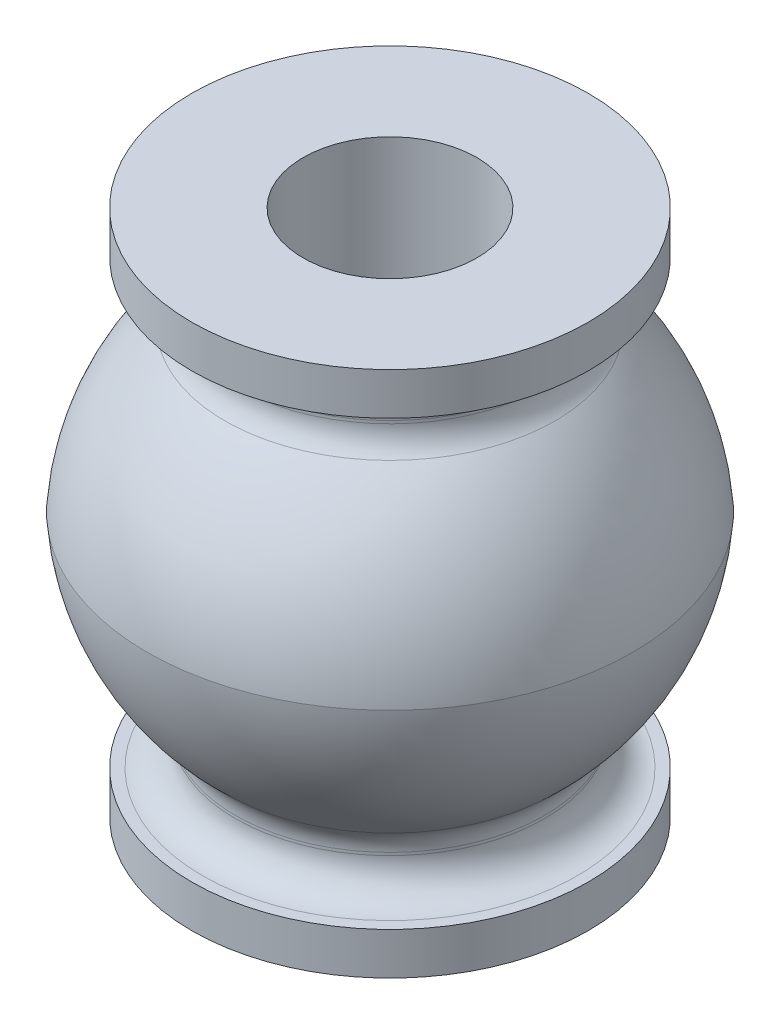
SolidWorks part; units mm, degrees
material "Rubber"
ref_plane "Front" through (0, 0, 0) normal (0, 0, 1) x (1, 0, 0)
ref_plane "Top" through (0, 0, 0) normal (0, 1, 0) x (1, 0, 0)
ref_plane "Right" through (0, 0, 0) normal (1, 0, 0) x (0, 0, -1)
sketch "Sketch2" plane through (0, 0, 0) normal (0, 0, 1) x (1, 0, 0)
  line L0 (0, -8) -> (0, 8) construction
  line L1 (0, 8) -> (2.64, 8) construction
  line L2 (2.64, 8) -> (6.02, 8)
  line L3 (6.02, 8) -> (6.02, 6.72)
  line L4 (6.02, 6.72) -> (4.69, 6.72)
  line L5 (4.69, 6.72) -> (4.69, 5.18)
  line L6 (0, 0) -> (7.375, 0) construction
  line L7 (2.64, 8) -> (2.64, 4.0052)
  line L8 (3.7256, 4.0052) -> (2.64, 4.0052)
  line L9 (0, -8) -> (2.64, -8) construction
  line L10 (3.7256, -4.0052) -> (2.64, -4.0052)
  line L11 (2.64, -8) -> (2.64, -4.0052)
  line L12 (4.69, -6.72) -> (4.69, -5.18)
  line L13 (6.02, -6.72) -> (4.69, -6.72)
  line L14 (6.02, -8) -> (6.02, -6.72)
  line L15 (2.64, -8) -> (6.02, -8)
  arc A0 (4.69, 5.18) -> (7.375, 0) centre (-0.0053, -0.5396) cw
  arc A1 (3.7256, 4.0052) -> (5.8499, 0) centre (-0.0053, -0.5396) cw
  arc A2 (3.7256, 4.0052) -> (5.859, -0.1108) centre (-0.0053, -0.5396) cw construction
  arc A3 (3.7256, -4.0052) -> (5.8499, 0) centre (-0.0053, 0.5396) ccw
  arc A4 (4.69, -5.18) -> (7.375, 0) centre (-0.0053, 0.5396) ccw
  dimension "D7" = 7.4
  dimension "D1" = 6.02
  dimension "D2" = 8
  dimension "D3" = 2.64
  dimension "D4" = 9.38
  dimension "D5" = 1.28
  dimension "D6" = 7.375
  dimension "D8" = 1.54
  dimension "D9" = 1.52
revolve "Revolve1" add sketch "Sketch2" angle 360 about L0
fillet "Fillet1" radius 1 4 edges at (0, -6.72, -4.69) (0, -5.18, -4.69) (0, 5.18, -4.69) (0, 6.72, -4.69)
